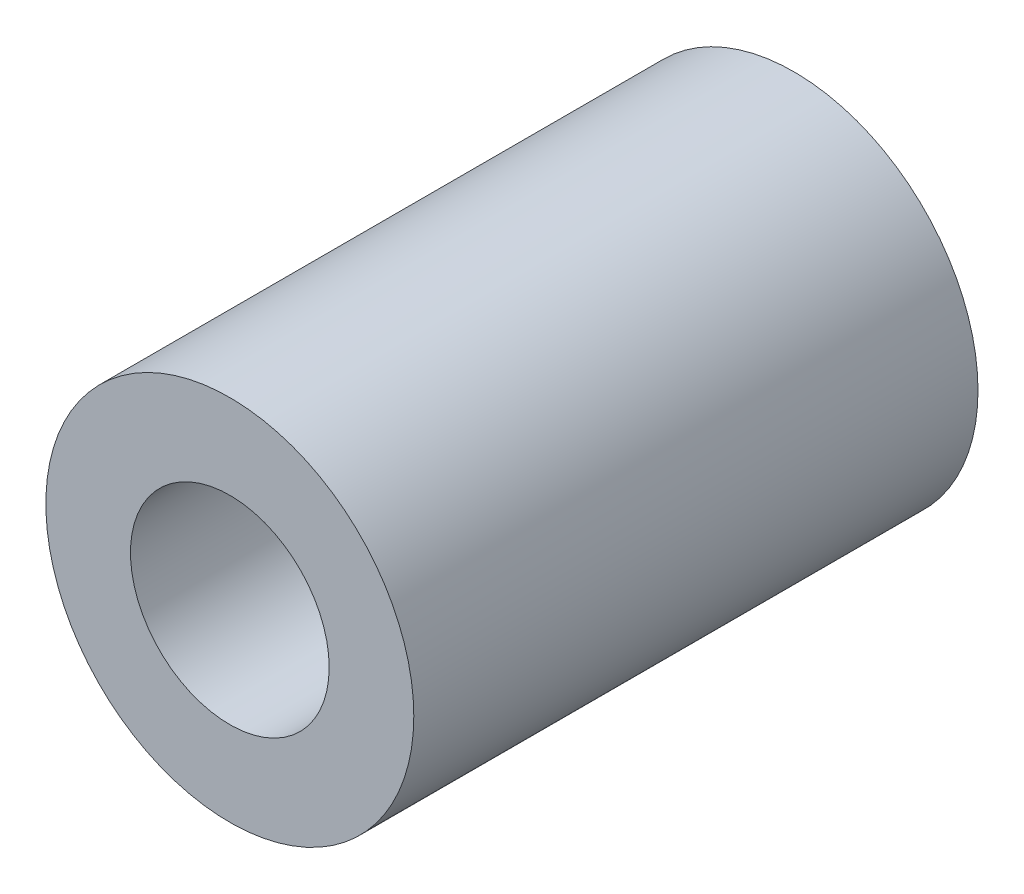
SolidWorks part; units mm, degrees
material "PBT General Purpose"
ref_plane "Plane1" through (0, 0, 0) normal (0, 0, 1) x (1, 0, 0)
ref_plane "Plane2" through (0, 0, 0) normal (0, 1, 0) x (1, 0, 0)
ref_plane "Plane3" through (0, 0, 0) normal (1, 0, 0) x (0, 0, -1)
sketch "Sketch1" plane through (0, 0, 0) normal (0, 0, 1) x (1, 0, 0)
  circle A0 centre (0, 0) radius 7.5
  dimension "D1" = 15
extrude "Boss-Extrude1" add sketch "Sketch1" along normal blind 23
sketch "Sketch2" plane through (0, 0, 23) normal (0, 0, 1) x (1, 0, 0)
  circle A0 centre (0, 0) radius 4.05
  dimension "D1" = 8.1
extrude "Cut-Extrude1" cut sketch "Sketch2" against normal through all
